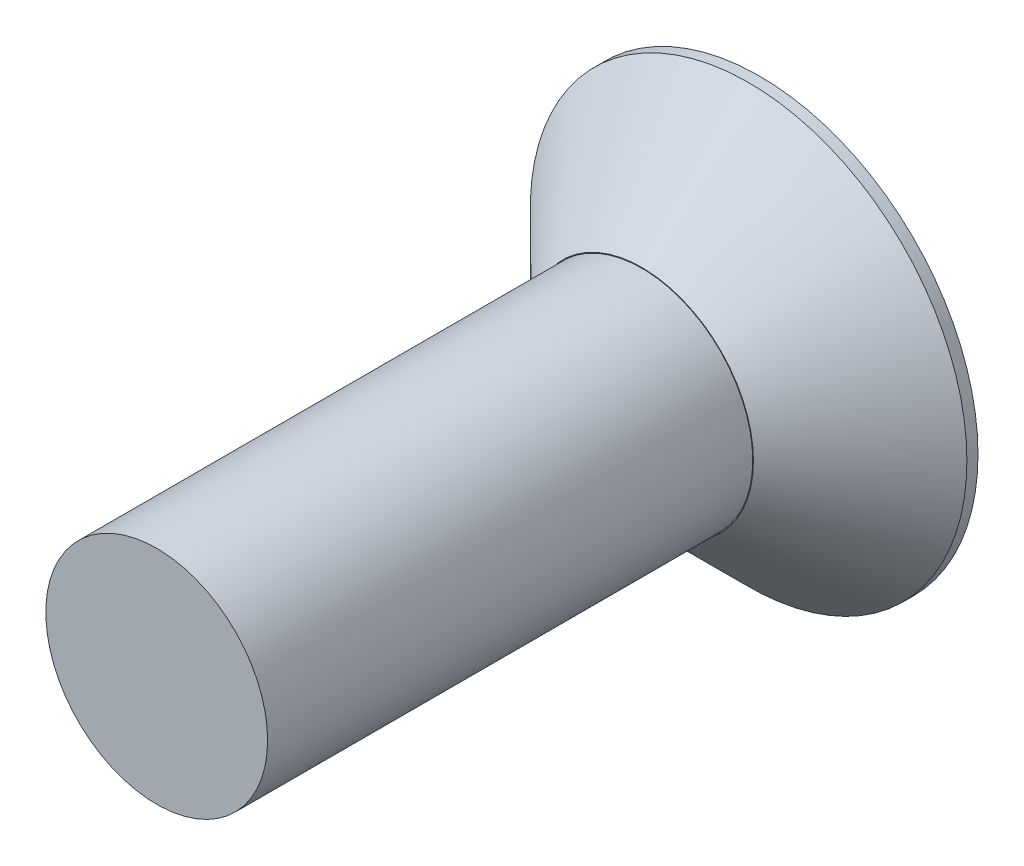
SolidWorks part; units mm, degrees
ref_plane "Front Plane" through (0, 0, 0) normal (0, 0, 1) x (1, 0, 0)
ref_plane "Top Plane" through (0, 0, 0) normal (0, 1, 0) x (1, 0, 0)
ref_plane "Right Plane" through (0, 0, 0) normal (1, 0, 0) x (0, 0, -1)
sketch "Sketch1" plane through (0, 0, 0) normal (0, 0, 1) x (1, 0, 0)
  circle A0 centre (0, 0) radius 4.0005
  dimension "D1" = 8.001
extrude "Extrude1" add sketch "Sketch1" along normal blind 2.159
sketch "Sketch2" plane through (0, 0, 2.159) normal (0, 0, 1) x (1, 0, 0)
  circle A0 centre (0, 0) radius 2.032
extrude "Extrude2" add sketch "Sketch2" along normal blind 8.89
sketch "Sketch3" plane through (0, 0, 0) normal (0, 0, -1) x (-1, 0, 0)
  line L1 (2.54, 0.254) -> (-2.54, 0.254)
  line L2 (2.54, 0.254) -> (2.54, -0.254)
  line L3 (2.54, -0.254) -> (-2.54, -0.254)
  line L4 (-2.54, 0.254) -> (-2.54, -0.254)
  line L5 (2.54, 0.254) -> (-2.54, -0.254) construction
  line L6 (2.54, -0.254) -> (-2.54, 0.254) construction
  point P0 (0, 0)
extrude "Extrude3" cut sketch "Sketch3" against normal blind 1.016
pattern_circular "CirPattern1" count 2 over 90 about axis through (0, 0, 0) along (0, 0, 1) of "Extrude3"
chamfer "Chamfer1" distance 1.9558 angle 45 1 edges at (4.0005, 0, 2.159)
